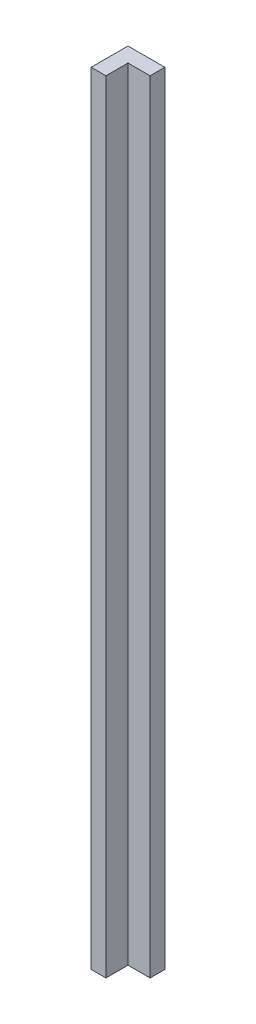
SolidWorks part; units mm, degrees
material "2014-T6"
ref_plane "Front Plane" through (0, 0, 0) normal (0, 0, 1) x (1, 0, 0)
ref_plane "Top Plane" through (0, 0, 0) normal (0, 1, 0) x (1, 0, 0)
ref_plane "Right Plane" through (0, 0, 0) normal (1, 0, 0) x (0, 0, -1)
sketch "Sketch1" plane through (0, 0, 0) normal (0, 1, 0) x (1, 0, 0)
  line L0 (-1.5928, 1.7032) -> (2.1385, 1.7032)
  line L9 (2.1385, 1.7032) -> (2.1385, -0.2968)
  line L10 (2.1385, -0.2968) -> (-0.8615, -0.2968)
  line L11 (-0.8615, -0.2968) -> (-0.8615, -3.2968)
  line L12 (-0.8615, -3.2968) -> (-2.8615, -3.2968)
  line L13 (-2.8615, -3.2968) -> (-2.8615, 1.7032)
  line L14 (-2.8615, 1.7032) -> (-1.5928, 1.7032)
  dimension "D1" = 2
  dimension "D2" = 2
  dimension "D3" = 5
  dimension "D4" = 5
extrude "Boss-Extrude1" add sketch "Sketch1" along normal blind 106
